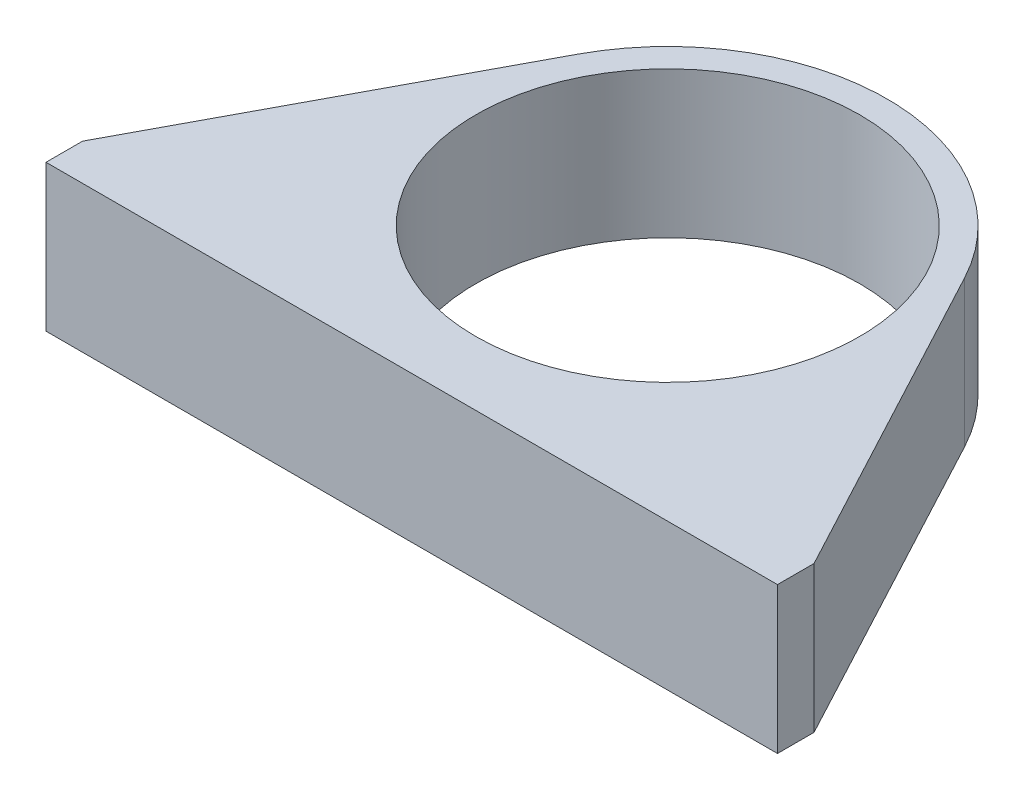
SolidWorks part; units mm, degrees
ref_plane "Front Plane" through (0, 0, 0) normal (0, 0, 1) x (1, 0, 0)
ref_plane "Top Plane" through (0, 0, 0) normal (0, 1, 0) x (1, 0, 0)
ref_plane "Right Plane" through (0, 0, 0) normal (1, 0, 0) x (0, 0, -1)
sketch "Sketch1" plane through (0, 0, 0) normal (0, 1, 0) x (1, 0, 0)
  line L2 (-50, -30) -> (-50, -35)
  line L3 (50, -30) -> (50, -35)
  line L4 (-50, -35) -> (50, -35)
  line L5 (-50, -30) -> (-26.4706, 14.1176)
  line L6 (50, -30) -> (26.4706, 14.1176)
  circle A0 centre (0, 0) radius 30
extrude "Boss-Extrude1" add sketch "Sketch1" along normal blind 20 contours A0 | A0 L5 L2 L4 L3 L6
sketch "Sketch2" plane through (0, 0, 0) normal (0, 1, 0) x (1, 0, 0)
  circle A0 centre (0, 0) radius 26.25
extrude "Cut-Extrude1" cut sketch "Sketch2" along normal blind 20
